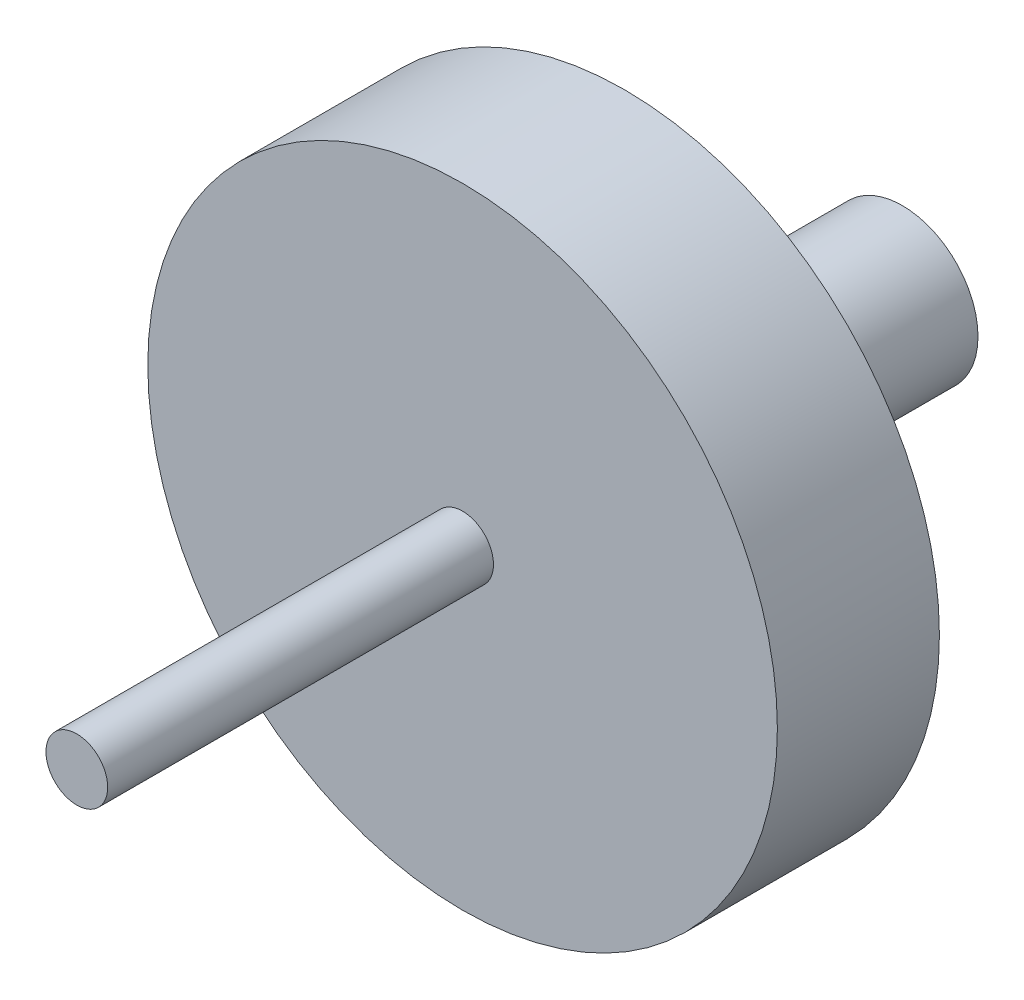
SolidWorks part; units mm, degrees
ref_plane "Front Plane" through (0, 0, 0) normal (0, 0, 1) x (1, 0, 0)
ref_plane "Top Plane" through (0, 0, 0) normal (0, 1, 0) x (1, 0, 0)
ref_plane "Right Plane" through (0, 0, 0) normal (1, 0, 0) x (0, 0, -1)
sketch "Sketch1" plane through (0, 0, 0) normal (0, 1, 0) x (1, 0, 0)
  line L0 (4.9, 0) -> (0, 0)
  line L1 (0, 0) -> (0, -53.5)
  line L2 (0, -53.5) -> (2, -53.5)
  line L3 (2, -53.5) -> (2, -28.5)
  line L4 (2, -28.5) -> (20.4, -28.5)
  line L5 (20.4, -28.5) -> (20.4, -18)
  line L6 (20.4, -18) -> (4.9, -18)
  line L7 (4.9, -18) -> (4.9, 0)
  line L8 (0, 0) -> (0, -53.5) construction
  dimension "D1" = 2
  dimension "D2" = 4.9
  dimension "D3" = 20.4
  dimension "D4" = 25
  dimension "D5" = 35.5
  dimension "D6" = 53.5
revolve "Revolve1" add sketch "Sketch1" angle 360 about L8
